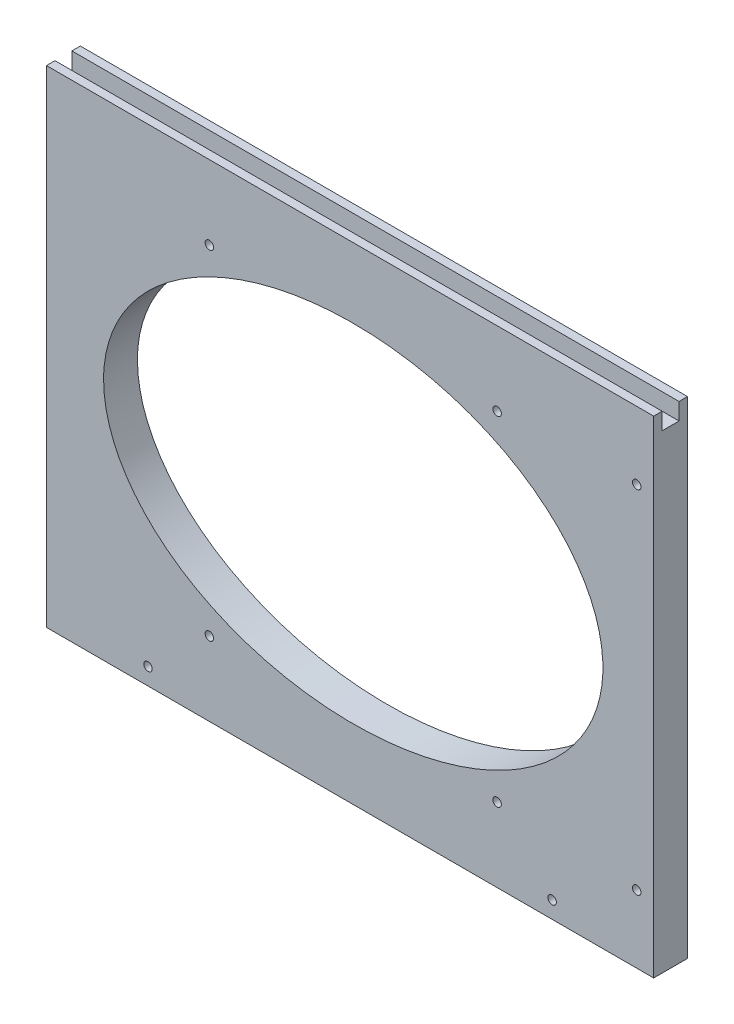
SolidWorks part; units mm, degrees
material "Pine"
ref_plane "Front Plane" through (0, 0, 0) normal (0, 0, 1) x (1, 0, 0)
ref_plane "Top Plane" through (0, 0, 0) normal (0, 1, 0) x (1, 0, 0)
ref_plane "Right Plane" through (0, 0, 0) normal (1, 0, 0) x (0, 0, -1)
sketch "Sketch1" plane through (0, 0, 0) normal (0, 0, 1) x (1, 0, 0)
  line L0 (-5300.6625, 1520.825) -> (-5451.475, 1520.825)
  line L1 (-5456.2375, 1384.3) -> (-5456.2375, 1516.0625)
  line L2 (-5557.8375, 1546.225) -> (-5194.3, 1546.225)
  line L3 (-5557.8375, 1539.875) -> (-5194.3, 1539.875)
  line L4 (-5297.4875, 1377.95) -> (-5454.65, 1377.95)
  line L5 (-5291.1375, 1384.3) -> (-5291.1375, 1516.0625)
  line L6 (-5300.6625, 1525.5875) -> (-5451.475, 1525.5875)
  line L7 (-5461, 1384.3) -> (-5461, 1516.0625)
  line L8 (-5297.4875, 1382.7125) -> (-5454.65, 1382.7125)
  line L9 (-5295.9, 1384.3) -> (-5295.9, 1516.0625)
  line L10 (-5740.4, 998.5375) -> (-5740.4, 1181.1)
  line L11 (-5740.4, 1181.1) -> (-5512.5938, 1181.1)
  line L12 (-5512.5938, 1181.1) -> (-5512.5938, 998.5375)
  line L13 (-5512.5938, 998.5375) -> (-5740.4, 998.5375)
  line L14 (-5258.5938, 1181.1) -> (-5486.4, 1181.1)
  line L15 (-5258.5938, 998.5375) -> (-5258.5938, 1181.1)
  line L16 (-5486.4, 998.5375) -> (-5258.5938, 998.5375)
  line L17 (-5486.4, 1181.1) -> (-5486.4, 998.5375)
  line L18 (-5740.4, 898.525) -> (-5011.7375, 898.525)
  line L19 (-5168.1062, 1384.3) -> (-5168.1062, 1392.2375)
  line L20 (-5176.0437, 1400.175) -> (-5245.8937, 1400.175)
  line L21 (-5253.8313, 1392.2375) -> (-5253.8313, 1384.3)
  line L22 (-5451.475, 1512.8875) -> (-5451.475, 1384.3)
  line L23 (-5303.8375, 1516.0625) -> (-5448.3, 1516.0625)
  line L24 (-5498.3062, 1384.3) -> (-5451.475, 1384.3)
  line L25 (-5253.8313, 1384.3) -> (-5300.6625, 1384.3)
  line L26 (-5584.0312, 1384.3) -> (-5740.4, 1384.3)
  line L27 (-5564.1875, 1536.7) -> (-5740.4, 1536.7)
  line L28 (-5740.4, 1357.3125) -> (-5740.4, 1206.5)
  line L29 (-5011.7375, 1357.3125) -> (-5740.4, 1357.3125)
  line L30 (-5011.7375, 1206.5) -> (-5011.7375, 1357.3125)
  line L31 (-5740.4, 1206.5) -> (-5011.7375, 1206.5)
  line L32 (-4765.675, 1549.4) -> (-4978.4, 1549.4)
  line L33 (-4765.675, 1397) -> (-4765.675, 1549.4)
  line L34 (-4978.4, 1397) -> (-4765.675, 1397)
  line L35 (-4978.4, 1549.4) -> (-4978.4, 1397)
  line L36 (-4765.675, 1371.6) -> (-4978.4, 1371.6)
  line L37 (-4765.675, 1219.2) -> (-4765.675, 1371.6)
  line L38 (-4978.4, 1219.2) -> (-4765.675, 1219.2)
  line L39 (-4978.4, 1371.6) -> (-4978.4, 1219.2)
  line L40 (-5284.7875, 803.275) -> (-5272.0875, 803.275)
  line L41 (-5187.95, 1536.7) -> (-5011.7375, 1536.7)
  line L42 (-5300.6625, 1384.3) -> (-5300.6625, 1512.8875)
  line L43 (-5740.4, 1536.7) -> (-5740.4, 1384.3)
  line L44 (-5557.8375, 1536.7) -> (-5557.8375, 1549.4)
  line L45 (-5557.8375, 1549.4) -> (-5194.3, 1549.4)
  line L46 (-5194.3, 1549.4) -> (-5194.3, 1536.7)
  line L47 (-5011.7375, 1536.7) -> (-5011.7375, 1384.3)
  line L48 (-5011.7375, 1384.3) -> (-5168.1062, 1384.3)
  line L49 (-5498.3062, 1384.3) -> (-5498.3062, 1392.2375)
  line L50 (-5506.2437, 1400.175) -> (-5576.0938, 1400.175)
  line L51 (-5584.0312, 1392.2375) -> (-5584.0312, 1384.3)
  line L52 (-5740.4, 660.4) -> (-5740.4, 898.525)
  line L53 (-5011.7375, 898.525) -> (-5011.7375, 660.4)
  line L54 (-5011.7375, 660.4) -> (-5740.4, 660.4)
  line L55 (-5291.1375, 803.275) -> (-5291.1375, 752.475)
  line L56 (-5265.7375, 752.475) -> (-5265.7375, 803.275)
  line L57 (-5284.7875, 752.475) -> (-5272.0875, 752.475)
  arc A0 (-5451.475, 1520.825) -> (-5456.2375, 1516.0625) centre (-5451.475, 1516.0625) ccw
  arc A1 (-5461, 1384.3) -> (-5454.65, 1377.95) centre (-5454.65, 1384.3) ccw
  arc A2 (-5297.4875, 1377.95) -> (-5291.1375, 1384.3) centre (-5297.4875, 1384.3) ccw
  circle A3 centre (-5037.9312, 1233.4875) radius 1.5875
  circle A4 centre (-5037.9312, 1328.7375) radius 1.5875
  circle A5 centre (-5714.2063, 1233.4875) radius 1.5875
  circle A6 centre (-5714.2063, 1328.7375) radius 1.5875
  circle A7 centre (-5018.0875, 1333.5) radius 1.5875
  circle A8 centre (-5018.0875, 1231.9) radius 1.5875
  circle A9 centre (-5734.05, 1231.9) radius 1.5875
  circle A10 centre (-5734.05, 1333.5) radius 1.5875
  circle A11 centre (-5734.05, 1511.3) radius 1.5875
  circle A12 centre (-5734.05, 1409.7) radius 1.5875
  circle A13 centre (-5018.0875, 1511.3) radius 1.5875
  circle A14 centre (-5018.0875, 1409.7) radius 1.5875
  arc A15 (-5557.8375, 1546.225) -> (-5557.8375, 1539.875) centre (-5557.8375, 1543.05) ccw
  arc A16 (-5194.3, 1539.875) -> (-5194.3, 1546.225) centre (-5194.3, 1543.05) ccw
  arc A17 (-5291.1375, 1516.0625) -> (-5300.6625, 1525.5875) centre (-5300.6625, 1516.0625) ccw
  arc A18 (-5451.475, 1525.5875) -> (-5461, 1516.0625) centre (-5451.475, 1516.0625) ccw
  arc A19 (-5456.2375, 1384.3) -> (-5454.65, 1382.7125) centre (-5454.65, 1384.3) ccw
  arc A20 (-5297.4875, 1382.7125) -> (-5295.9, 1384.3) centre (-5297.4875, 1384.3) ccw
  arc A21 (-5295.9, 1516.0625) -> (-5300.6625, 1520.825) centre (-5300.6625, 1516.0625) ccw
  circle A22 centre (-5702.3, 892.175) radius 1.5875
  circle A23 centre (-5734.05, 860.425) radius 1.5875
  circle A24 centre (-5474.8906, 892.175) radius 1.5875
  circle A25 centre (-5277.2469, 892.175) radius 1.5875
  circle A26 centre (-5049.8375, 892.175) radius 1.5875
  circle A27 centre (-5018.0875, 860.425) radius 1.5875
  circle A28 centre (-5296.6938, 1174.75) radius 1.5875
  circle A29 centre (-5448.3, 1174.75) radius 1.5875
  circle A30 centre (-5264.9437, 1155.7) radius 1.5875
  circle A31 centre (-5264.9437, 1023.9375) radius 1.5875
  circle A32 centre (-5518.9438, 1155.7) radius 1.5875
  circle A33 centre (-5518.9438, 1023.9375) radius 1.5875
  circle A34 centre (-5702.3, 1004.8875) radius 1.5875
  circle A35 centre (-5550.6937, 1004.8875) radius 1.5875
  arc A36 (-5576.0938, 1400.175) -> (-5584.0312, 1392.2375) centre (-5576.0938, 1392.2375) ccw
  arc A37 (-5168.1062, 1392.2375) -> (-5176.0437, 1400.175) centre (-5176.0437, 1392.2375) ccw
  arc A38 (-5245.8937, 1400.175) -> (-5253.8313, 1392.2375) centre (-5245.8937, 1392.2375) ccw
  arc A39 (-5448.3, 1516.0625) -> (-5451.475, 1512.8875) centre (-5448.3, 1512.8875) ccw
  arc A40 (-5284.7875, 803.275) -> (-5291.1375, 803.275) centre (-5287.9625, 803.275) ccw
  circle A41 centre (-5679.2812, 1026.3187) radius 1.5875
  circle A42 centre (-5679.2812, 1153.3187) radius 1.5875
  circle A43 centre (-5571.3313, 1153.3187) radius 1.5875
  circle A44 centre (-5571.3313, 1026.3187) radius 1.5875
  circle A45 centre (-5317.3312, 1153.3187) radius 1.5875
  circle A46 centre (-5317.3312, 1026.3187) radius 1.5875
  circle A47 centre (-5425.2812, 1026.3187) radius 1.5875
  circle A48 centre (-5425.2812, 1153.3187) radius 1.5875
  arc A49 (-5194.3, 1536.7) -> (-5187.95, 1536.7) centre (-5191.125, 1536.7) ccw
  arc A50 (-5564.1875, 1536.7) -> (-5557.8375, 1536.7) centre (-5561.0125, 1536.7) ccw
  arc A51 (-5300.6625, 1512.8875) -> (-5303.8375, 1516.0625) centre (-5303.8375, 1512.8875) ccw
  arc A52 (-5498.3062, 1392.2375) -> (-5506.2437, 1400.175) centre (-5506.2437, 1392.2375) ccw
  circle A53 centre (-5712.46, 784.225) radius 4.7625
  arc A54 (-5272.0875, 752.475) -> (-5265.7375, 752.475) centre (-5268.9125, 752.475) ccw
  arc A55 (-5291.1375, 752.475) -> (-5284.7875, 752.475) centre (-5287.9625, 752.475) ccw
  circle A56 centre (-5182.3938, 684.2125) radius 3.175
  circle A57 centre (-5239.5437, 684.2125) radius 3.175
  circle A58 centre (-5512.5938, 684.2125) radius 3.175
  circle A59 centre (-5569.7437, 684.2125) radius 3.175
  circle A60 centre (-5474.8906, 666.75) radius 1.5875
  circle A61 centre (-5277.2469, 666.75) radius 1.5875
  circle A62 centre (-5734.05, 698.5) radius 1.5875
  circle A63 centre (-5702.3, 666.75) radius 1.5875
  circle A64 centre (-5049.8375, 666.75) radius 1.5875
  circle A65 centre (-5018.0875, 698.5) radius 1.5875
  circle A66 centre (-5713.73, 835.025) radius 4.7625
  circle A67 centre (-5712.46, 819.785) radius 4.7625
  circle A68 centre (-5712.46, 802.005) radius 4.7625
  circle A69 centre (-5714.2063, 1314.45) radius 3.175
  circle A70 centre (-5037.9312, 1314.45) radius 3.175
  arc A71 (-5265.7375, 803.275) -> (-5272.0875, 803.275) centre (-5268.9125, 803.275) ccw
  ellipse E0 centre (-5371.3062, 1089.8188) end of major axis (-5277.6438, 1089.8188) minor radius 65.0875
  ellipse E1 centre (-5625.3062, 1089.8188) end of major axis (-5531.6438, 1089.8188) minor radius 65.0875
sketch "Sketch2" plane through (0, 0, 0) normal (0, 0, 1) x (1, 0, 0)
  line L0 (-5512.5938, 998.5375) -> (-5512.5938, 1181.1)
  line L1 (-5512.5938, 1181.1) -> (-5740.4, 1181.1)
  line L2 (-5740.4, 1181.1) -> (-5740.4, 998.5375)
  line L3 (-5740.4, 998.5375) -> (-5512.5938, 998.5375)
extrude "Extrude1" add sketch "Sketch2" against normal blind 12.7
sketch "Sketch4" plane through (0, 0, 0) normal (0, 0, 1) x (1, 0, 0)
  line L0 (-5625.3062, 1154.9062) -> (-5625.3062, 1024.7313) construction
  line L1 (-5718.9687, 1089.8188) -> (-5531.6438, 1089.8188) construction
  circle A0 centre (-5571.3313, 1153.3187) radius 1.5875
  circle A1 centre (-5518.9438, 1155.7) radius 1.5875
  circle A2 centre (-5518.9438, 1023.9375) radius 1.5875
  circle A3 centre (-5550.6937, 1004.8875) radius 1.5875
  circle A4 centre (-5571.3313, 1026.3187) radius 1.5875
  circle A5 centre (-5679.2812, 1026.3187) radius 1.5875
  circle A6 centre (-5702.3, 1004.8875) radius 1.5875
  circle A7 centre (-5679.2812, 1153.3187) radius 1.5875
  ellipse E0 centre (-5625.3062, 1089.8188) end of major axis (-5718.9687, 1089.8188) minor radius 65.0875
extrude "Cut-Extrude1" cut sketch "Sketch4" against normal up to surface (12.7 mm away) up to face at (-5626.4969, 1089.8188, -12.7)
sketch "Sketch5" plane through (-5512.5938, 0, 0) normal (1, 0, 0) x (0, 0, -1)
  line L0 (6.35, 1181.1) -> (3.175, 1181.1)
  line L1 (12.7, 1181.1) -> (0, 1181.1) construction
  line L2 (3.175, 1181.1) -> (3.175, 1174.75)
  line L3 (3.175, 1174.75) -> (9.525, 1174.75)
  line L4 (9.525, 1174.75) -> (9.525, 1181.1)
  line L5 (9.525, 1181.1) -> (6.35, 1181.1)
extrude "Cut-Extrude2" cut sketch "Sketch5" against normal up to surface (227.8063 mm away) up to face at (-5740.4, 1089.8188, -6.35)
